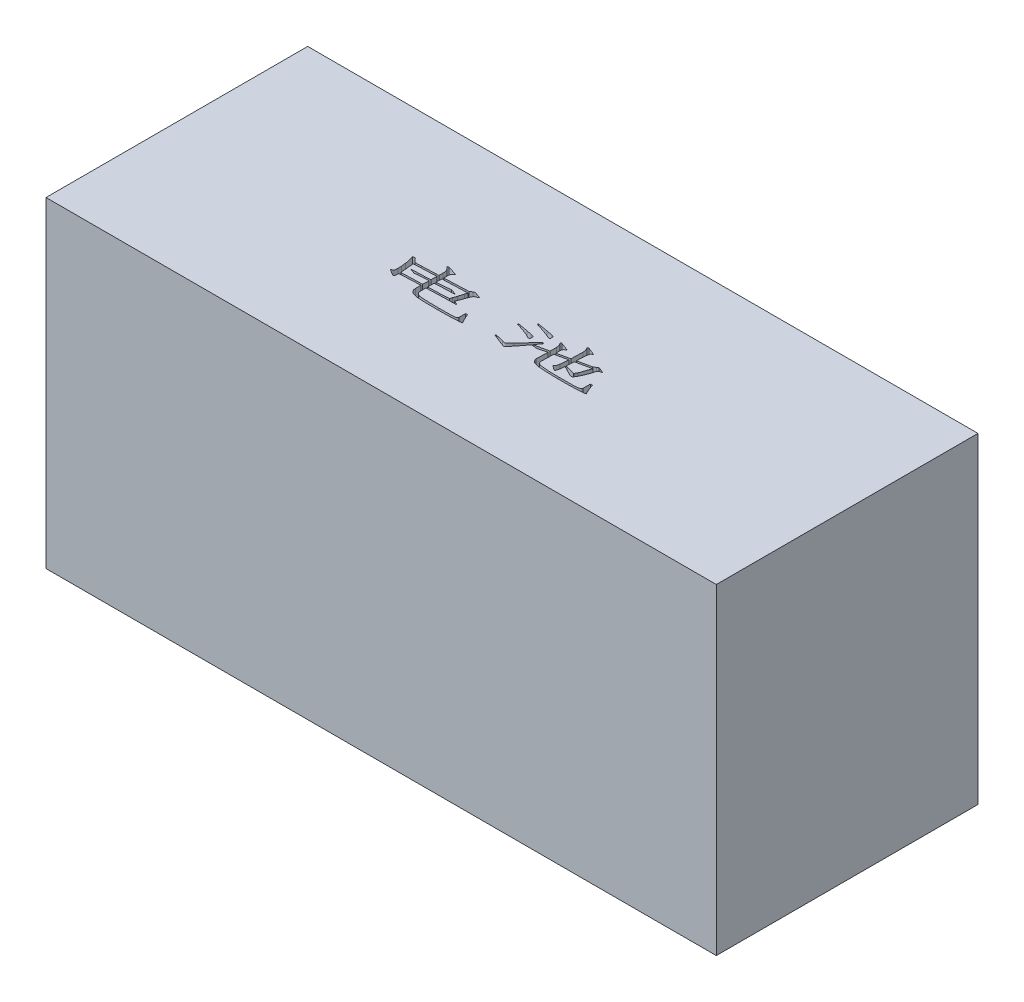
SolidWorks part; units mm, degrees
ref_plane "前视基准面" through (0, 0, 0) normal (0, 0, 1) x (1, 0, 0)
ref_plane "上视基准面" through (0, 0, 0) normal (0, 1, 0) x (1, 0, 0)
ref_plane "右视基准面" through (0, 0, 0) normal (1, 0, 0) x (0, 0, -1)
sketch "草图1" plane through (0, 0, 0) normal (0, 1, 0) x (1, 0, 0)
  line L1 (-36.5, 14.25) -> (36.5, 14.25)
  line L2 (-36.5, 14.25) -> (-36.5, -14.25)
  line L3 (-36.5, -14.25) -> (36.5, -14.25)
  line L4 (36.5, 14.25) -> (36.5, -14.25)
  line L5 (-36.5, 14.25) -> (36.5, -14.25) construction
  line L6 (-36.5, -14.25) -> (36.5, 14.25) construction
  point P0 (0, 0)
  dimension "D1" = 73
  dimension "D2" = 28.5
extrude "凸台-拉伸1" add sketch "草图1" along normal blind 35
sketch "草图2" plane through (0, 35, 0) normal (0, 1, 0) x (1, 0, 0)
  text T0 "电池\r\n" font "汉仪长仿宋体" height 3.5
extrude "切除-拉伸1" cut sketch "草图2" against normal blind 35
